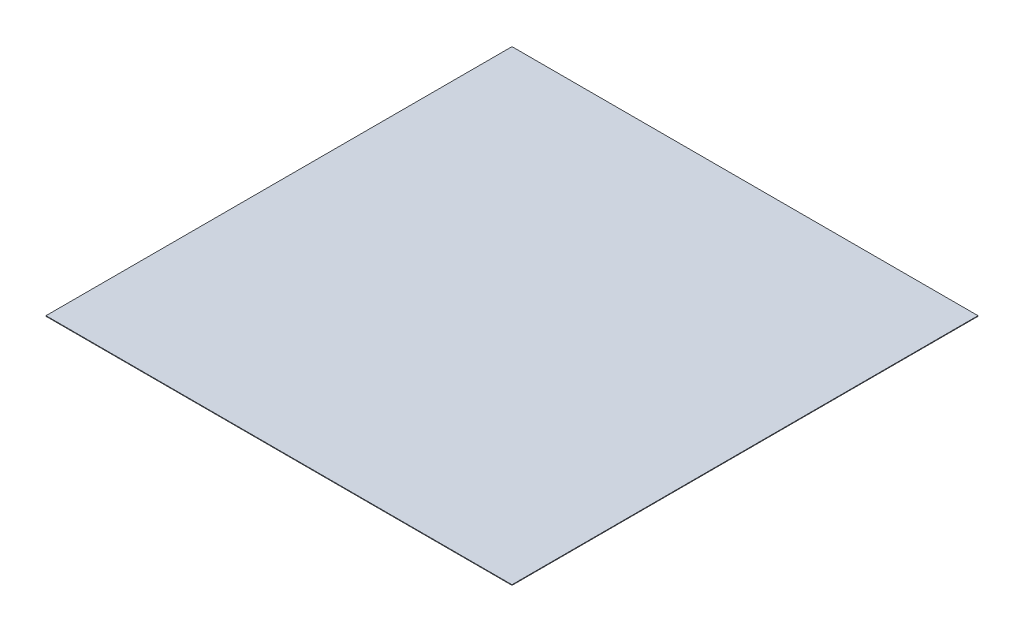
SolidWorks part; units mm, degrees
ref_plane "Front Plane" through (0, 0, 0) normal (0, 0, 1) x (1, 0, 0)
ref_plane "Top Plane" through (0, 0, 0) normal (0, 1, 0) x (1, 0, 0)
ref_plane "Right Plane" through (0, 0, 0) normal (1, 0, 0) x (0, 0, -1)
sketch "Sketch1" plane through (0, 0, 0) normal (0, 1, 0) x (1, 0, 0)
  line L1 (-391.414, 371.517) -> (408.586, 371.517)
  line L2 (-391.414, 371.517) -> (-391.414, -428.483)
  line L3 (-391.414, -428.483) -> (408.586, -428.483)
  line L4 (408.586, 371.517) -> (408.586, -428.483)
  dimension "D1" = 800
  dimension "D2" = 800
extrude "Boss-Extrude1" add sketch "Sketch1" along normal blind 1
